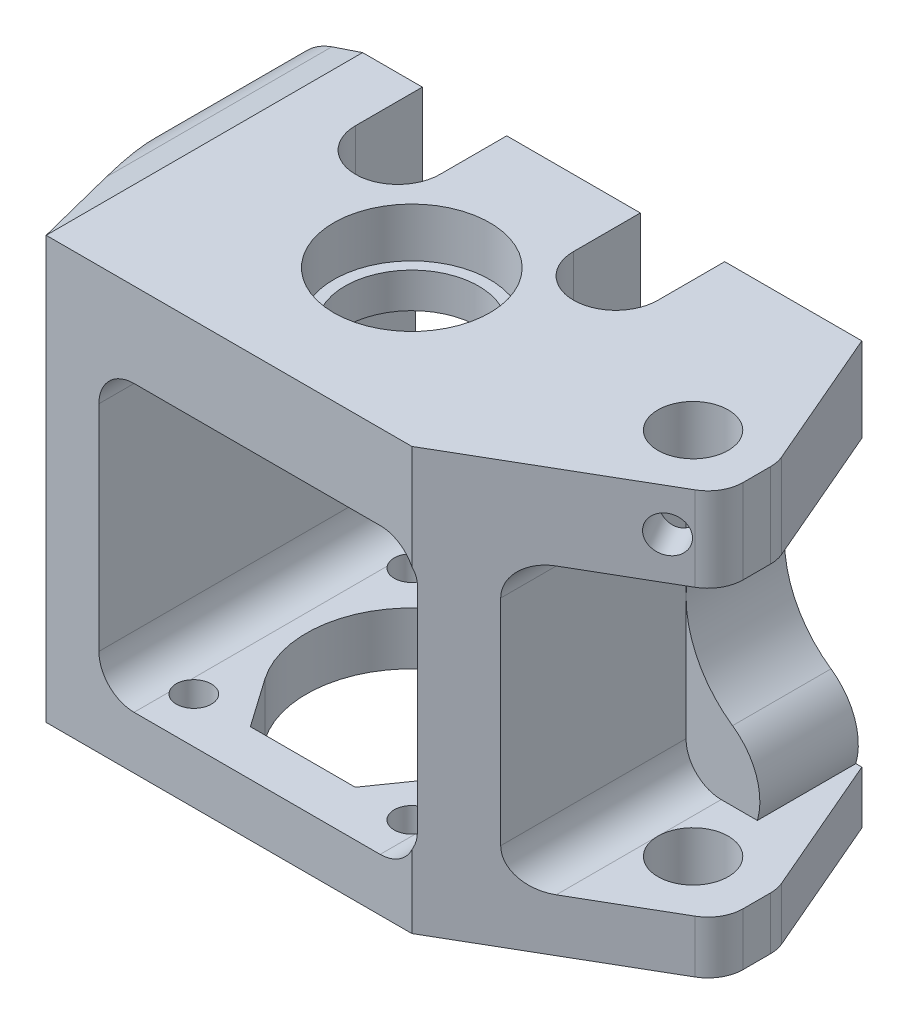
SolidWorks part; units mm, degrees
ref_plane "Front Plane" through (0, 0, 0) normal (0, 0, 1) x (1, 0, 0)
ref_plane "Top Plane" through (0, 0, 0) normal (0, 1, 0) x (1, 0, 0)
ref_plane "Right Plane" through (0, 0, 0) normal (1, 0, 0) x (0, 0, -1)
sketch "Sketch1" plane through (0, 0, 0) normal (0, 1, 0) x (1, 0, 0)
  line L0 (-30, 23) -> (41, 23)
  line L2 (41, 23) -> (50, 2.0578)
  line L3 (50, 2.0578) -> (50, -5.7603)
  line L4 (50, -5.7603) -> (22, -22)
  line L5 (22, -22) -> (-30, -22)
  line L6 (-30, -22) -> (-30, 23)
  circle A0 centre (0, 0) radius 9.5
  circle A1 centre (40, 0) radius 5
  dimension "D1" = 19
  dimension "D5" = 10
  dimension "D2" = 30
  dimension "D3" = 23
  dimension "D4" = 40
  dimension "D6" = 10
  dimension "D7" = 10
  dimension "D8" = 10
  dimension "D9" = 22
  dimension "D10" = 22
  dimension "D11" = 9
extrude "Boss-Extrude1" add sketch "Sketch1" along normal blind 60
sketch "Sketch2" plane through (0, 60, 0) normal (0, 1, 0) x (1, 0, 0)
  circle A0 centre (0, 0) radius 11.1
  dimension "D1" = 22.2
extrude "Cut-Extrude1" cut sketch "Sketch2" against normal blind 7
sketch "Sketch3" plane through (0, 0, 22) normal (0, 0, 1) x (1, 0, 0)
  line L0 (-30, 60) -> (22, 60) construction
  line L1 (-17.5, 48) -> (17.5, 48)
  line L2 (-22.5, 43) -> (-22.5, 12.5)
  line L3 (-17.5, 7.5) -> (17.5, 7.5)
  line L4 (22.5, 43) -> (22.5, 12.5)
  line L5 (35, 48) -> (66.371, 48)
  line L6 (30, 43) -> (30, 12.5)
  line L7 (35, 7.5) -> (66.371, 7.5)
  line L8 (66.371, 48) -> (66.371, 7.5)
  line L9 (-30, 0) -> (22, 0) construction
  line L10 (-30, 60) -> (-30, 0) construction
  arc A0 (-17.5, 48) -> (-22.5, 43) centre (-17.5, 43) ccw
  arc A1 (-22.5, 12.5) -> (-17.5, 7.5) centre (-17.5, 12.5) ccw
  arc A2 (17.5, 48) -> (22.5, 43) centre (17.5, 43) cw
  arc A3 (35, 48) -> (30, 43) centre (35, 43) ccw
  arc A4 (30, 12.5) -> (35, 7.5) centre (35, 12.5) ccw
  arc A5 (17.5, 7.5) -> (22.5, 12.5) centre (17.5, 12.5) ccw
  dimension "D6" = 5
  dimension "D1" = 12
  dimension "D2" = 7.5
  dimension "D3" = 7.5
  dimension "D4" = 22.5
  dimension "D5" = 7.5
extrude "Cut-Extrude2" cut sketch "Sketch3" against normal offset from surface (31 mm away) 14 up to face at (5.5, 30, -23)
sketch "Sketch4" plane through (0, 0, 0) normal (0, -1, 0) x (1, 0, 0)
  line L0 (-15.5, 15.5) -> (15.5, -15.5) construction
  line L1 (-12.2873, 8.6036) -> (-7.4584, 15.5)
  line L2 (-7.4584, 15.5) -> (7.4584, 15.5)
  line L3 (7.4584, 15.5) -> (12.2873, 8.6036)
  line L4 (0, 0) -> (0, 7.8623) construction
  arc A0 (-12.2873, 8.6036) -> (12.2873, 8.6036) centre (0, 0) ccw
  circle A1 centre (15.5, 15.5) radius 2.5
  circle A2 centre (-15.5, 15.5) radius 2.5
  circle A3 centre (-15.5, -15.5) radius 2.5
  circle A4 centre (15.5, -15.5) radius 2.5
  dimension "D2" = 30
  dimension "D3" = 5
  dimension "D1" = 31
  dimension "D4" = 31
  dimension "D5" = 15.5
  dimension "D6" = 35
  dimension "D7" = 35
extrude "Cut-Extrude3" cut sketch "Sketch4" against normal blind 16
sketch "Sketch7" plane through (0, 0, -23) normal (0, 0, -1) x (-1, 0, 0)
  line L0 (22.5, 43) -> (22.5, 12.5) construction
  line L1 (30, 60) -> (40.5, 60)
  line L2 (30, 60) -> (30, 0)
  line L3 (30, 0) -> (40.5, 0)
  line L4 (40.5, 60) -> (40.5, 0)
  dimension "D1" = 18
extrude "Boss-Extrude2" add sketch "Sketch7" against normal blind 14
sketch "Sketch8" plane through (0, 0, 0) normal (0, -1, 0) x (1, 0, 0)
  line L0 (-40.5, -9) -> (-30, 22)
  line L1 (-30, 22) -> (22, 22) construction
  line L2 (-30, -9) -> (-30, 22) construction
  line L3 (-30, 22) -> (-30, -9)
  line L4 (-30, -9) -> (-40.5, -9)
extrude "Boss-Extrude3" add sketch "Sketch8" against normal up to surface (60 mm away) up to face at (0, 60, 11.1)
sketch "Sketch5" plane through (0, 0, -23) normal (0, 0, -1) x (-1, 0, 0)
  line L0 (-41, 0) -> (40.5, 0) construction
  line L2 (-41, 60) -> (40.5, 60) construction
  line L4 (40.5, 0) -> (40.5, 60) construction
  circle A0 centre (31.5, 50) radius 4
  circle A1 centre (31.5, 10) radius 4
  circle A2 centre (-31.5, 10) radius 4
  circle A3 centre (-31.5, 50) radius 4
  dimension "D1" = 8
  dimension "D2" = 31.5
  dimension "D3" = 10
  dimension "D4" = 9
  dimension "D5" = 10
extrude "Cut-Extrude4" cut sketch "Sketch5" against normal blind 13
sketch "Sketch6" plane through (0, 0, -23) normal (0, 0, -1) x (-1, 0, 0)
  line L0 (-3.0414, 48) -> (-17.5, 48) construction
  line L1 (-22.5, 43) -> (-22.5, 12.5) construction
  line L2 (12, 7.5) -> (17.5, 7.5) construction
  line L3 (22.5, 12.5) -> (22.5, 43) construction
  line L4 (17.5, 48) -> (-17.5, 48)
  line L5 (-22.5, 43) -> (-22.5, 12.5)
  line L6 (-17.5, 7.5) -> (17.5, 7.5)
  line L7 (22.5, 12.5) -> (22.5, 43)
  line L9 (30, 60) -> (30, 0) construction
  line L10 (34.3692, 58.5304) -> (30, 60)
  line L11 (30, 60) -> (30, 65.6197)
  line L12 (30, 65.6197) -> (48.7488, 65.6197)
  line L13 (48.7488, 65.6197) -> (48.7488, -4.2346)
  line L14 (48.7488, -4.2346) -> (30, -4.2346)
  line L15 (30, -4.2346) -> (30, 0)
  line L16 (30, 0) -> (34.3692, 1.4696)
  line L17 (30, 60) -> (30, 0) construction
  line L18 (-41, 60) -> (40.5, 60) construction
  line L19 (-41, 0) -> (40.5, 0) construction
  line L20 (-30, 12.5) -> (-30, 43) construction
  line L21 (-30, 12.5) -> (-30, 43) construction
  line L22 (-50, 48) -> (-47.0166, 48) construction
  line L23 (-47.0166, 7.5) -> (-50, 7.5) construction
  line L24 (-50, 48) -> (-40.275, 48)
  line L25 (-40.1458, 7.5) -> (-50, 7.5)
  line L26 (-50, 48) -> (-50, 7.5)
  arc A0 (36.6107, 42.5919) -> (34.3692, 58.5304) centre (31.5, 50) ccw
  arc A1 (34.3692, 1.4696) -> (36.6107, 17.4081) centre (31.5, 10) ccw
  arc A2 (36.6107, 42.5919) -> (36.6107, 17.4081) centre (45.2976, 30) ccw
  arc A3 (-40.275, 48) -> (-36.6107, 42.5919) centre (-31.5, 50) ccw
  arc A4 (-36.6107, 17.4081) -> (-40.1458, 7.5) centre (-31.5, 10) ccw
  arc A5 (-36.6107, 17.4081) -> (-36.6107, 42.5919) centre (-45.2976, 30) ccw
  arc A12 (-22.5, 12.5) -> (-17.5, 7.5) centre (-17.5, 12.5) ccw
  arc A13 (17.5, 7.5) -> (22.5, 12.5) centre (17.5, 12.5) ccw
  arc A14 (22.5, 43) -> (17.5, 48) centre (17.5, 43) ccw
  arc A15 (-17.5, 48) -> (-22.5, 43) centre (-17.5, 43) ccw
  dimension "D1" = 18
  dimension "D3" = 5
extrude "Cut-Extrude5" cut sketch "Sketch6" against normal through all
fillet "Fillet1" radius 5 4 edges at (50, 3.75, -2.0578) (50, 3.75, 5.7603) (50, 54, -2.0578) (50, 54, 5.7603)
sketch "Sketch9" plane through (15.0856, 0, 26.0103) normal (0.5017, 0, 0.865) x (0.865, 0, -0.5017)
  line L0 (34.6014, 60) -> (34.6014, 48) construction
  circle A0 centre (34.6014, 54) radius 2.6
  dimension "D1" = 5.2
extrude "Cut-Extrude6" cut sketch "Sketch9" against normal blind 10
sketch "Sketch10" plane through (0, 60, 0) normal (0, 1, 0) x (1, 0, 0)
  line L0 (41, 23) -> (-30, 23) construction
  line L1 (21.5, 23) -> (9.5, 23)
  line L2 (-21.5, 13.5) -> (-21.5, 23)
  line L3 (-9.5, 13.5) -> (-9.5, 23)
  line L4 (9.5, 13.5) -> (9.5, 23)
  line L5 (21.5, 13.5) -> (21.5, 23)
  line L6 (-9.5, 23) -> (-21.5, 23)
  arc A0 (-21.5, 13.5) -> (-9.5, 13.5) centre (-15.5, 13.5) ccw
  arc A1 (9.5, 13.5) -> (21.5, 13.5) centre (15.5, 13.5) ccw
  dimension "D1" = 12
  dimension "D2" = 2
  dimension "D3" = 2
extrude "Cut-Extrude7" cut sketch "Sketch10" against normal blind 20
